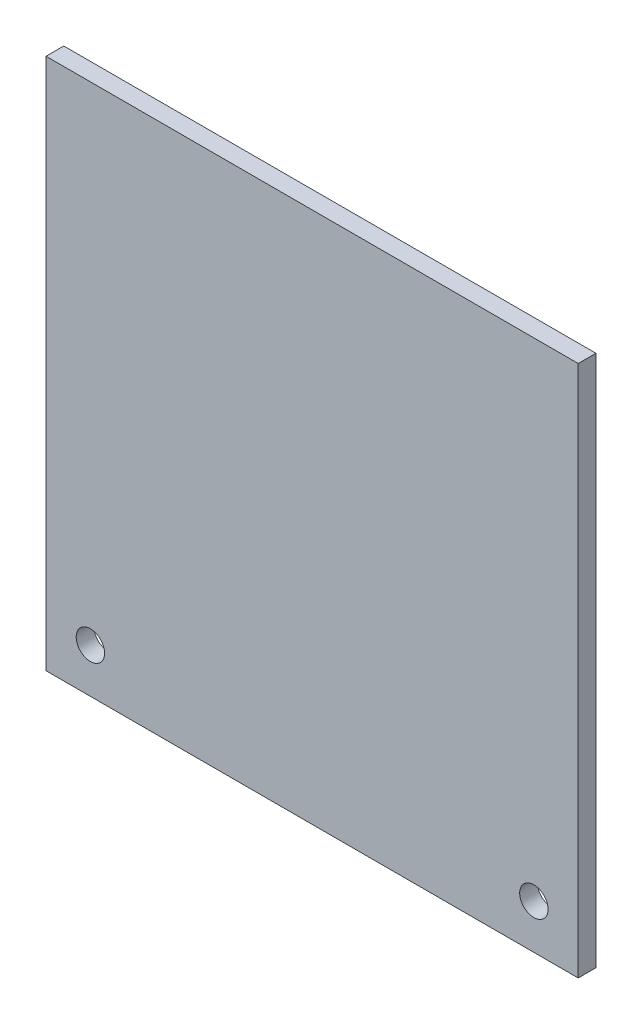
SolidWorks part; units mm, degrees
material "1060 Alloy"
ref_plane "Front Plane" through (0, 0, 0) normal (0, 0, 1) x (1, 0, 0)
ref_plane "Top Plane" through (0, 0, 0) normal (0, 1, 0) x (1, 0, 0)
ref_plane "Right Plane" through (0, 0, 0) normal (1, 0, 0) x (0, 0, -1)
sketch "Sketch1" plane through (0, 0, 0) normal (0, 0, 1) x (1, 0, 0)
  line L1 (0, 0) -> (60, 0)
  line L2 (0, 0) -> (0, 60)
  line L3 (0, 60) -> (60, 60)
  line L4 (60, 0) -> (60, 60)
  dimension "D1" = 60
  dimension "D2" = 60
extrude "Boss-Extrude1" add sketch "Sketch1" along normal blind 2
hole_wizard "M3 Clearance Hole1" positions "Sketch2" profile "Sketch3" hole size "M3" standard "ANSI Metric" end condition up to next
sketch "Sketch2" plane through (0, 0, 0) normal (0, 0, -1) x (-1, 0, 0)
  line L0 (-60, 5) -> (0, 5) construction
  line L1 (-60, 0) -> (-60, 60) construction
  line L2 (0, 60) -> (0, 0) construction
  line L3 (0, 0) -> (-60, 0) construction
  point P10 (-55, 5)
  point P12 (-5, 5)
  dimension "D1" = 5
  dimension "D2" = 5
  dimension "D3" = 5
sketch "Sketch3" plane through (55, 5, 0) normal (1, 0, 0) x (0, 1, 0)
  line L0 (0, 0) -> (0, 2)
  line L1 (0, 2) -> (1.6, 2)
  line L2 (1.6, 2) -> (1.6, 0)
  line L5 (1.6, 0) -> (0, 0)
  line L11 (0, -6.35) -> (0, 107.95) construction
  dimension "Thru Hole Dia." = 3.2
  dimension "Thru Hole Depth" = 2
